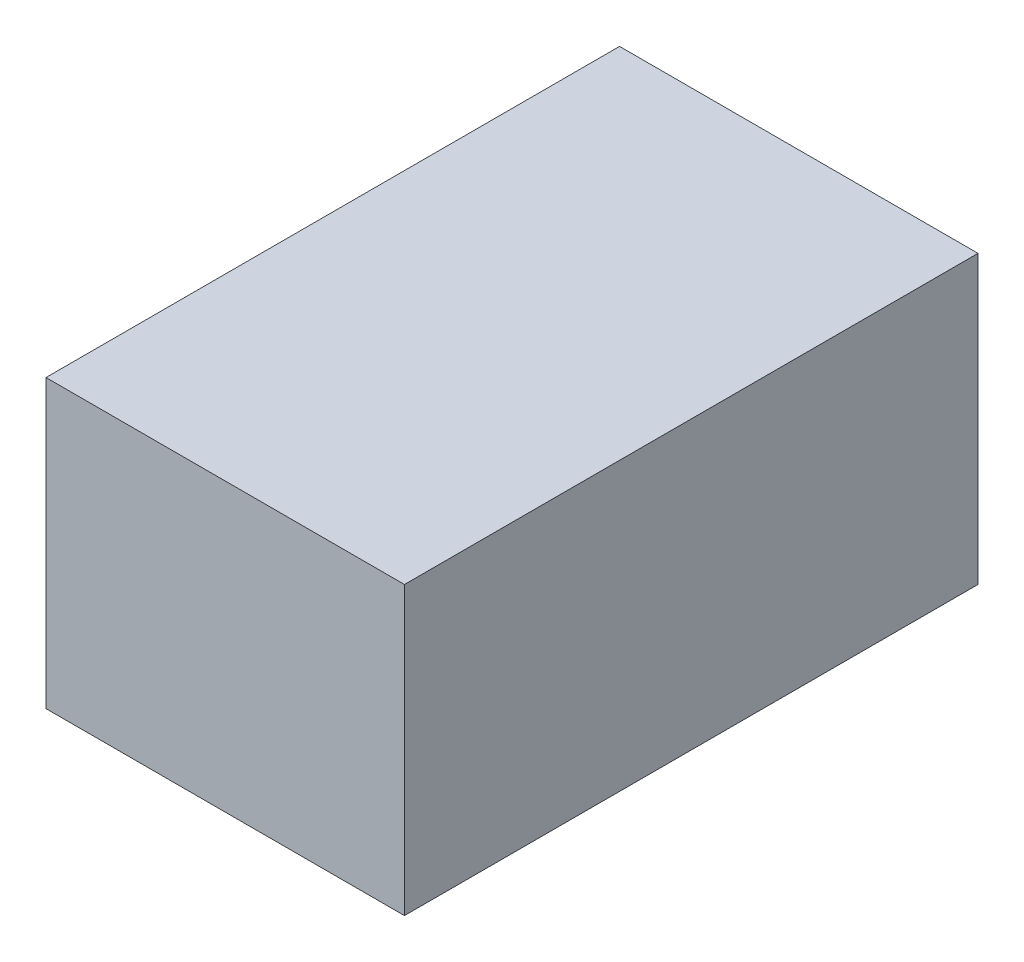
SolidWorks part; units mm, degrees
material "Cedar"
ref_plane "Front Plane" through (0, 0, 0) normal (0, 0, 1) x (1, 0, 0)
ref_plane "Top Plane" through (0, 0, 0) normal (0, 1, 0) x (1, 0, 0)
ref_plane "Right Plane" through (0, 0, 0) normal (1, 0, 0) x (0, 0, -1)
sketch "Sketch1" plane through (0, 0, 0) normal (0, 0, 1) x (1, 0, 0)
  line L1 (0, 0) -> (31.75, 0)
  line L2 (0, 0) -> (0, 25.4)
  line L3 (0, 25.4) -> (31.75, 25.4)
  line L4 (31.75, 0) -> (31.75, 25.4)
  dimension "D1" = 31.75
  dimension "D2" = 25.4
extrude "base" add sketch "Sketch1" against normal blind 50.8
